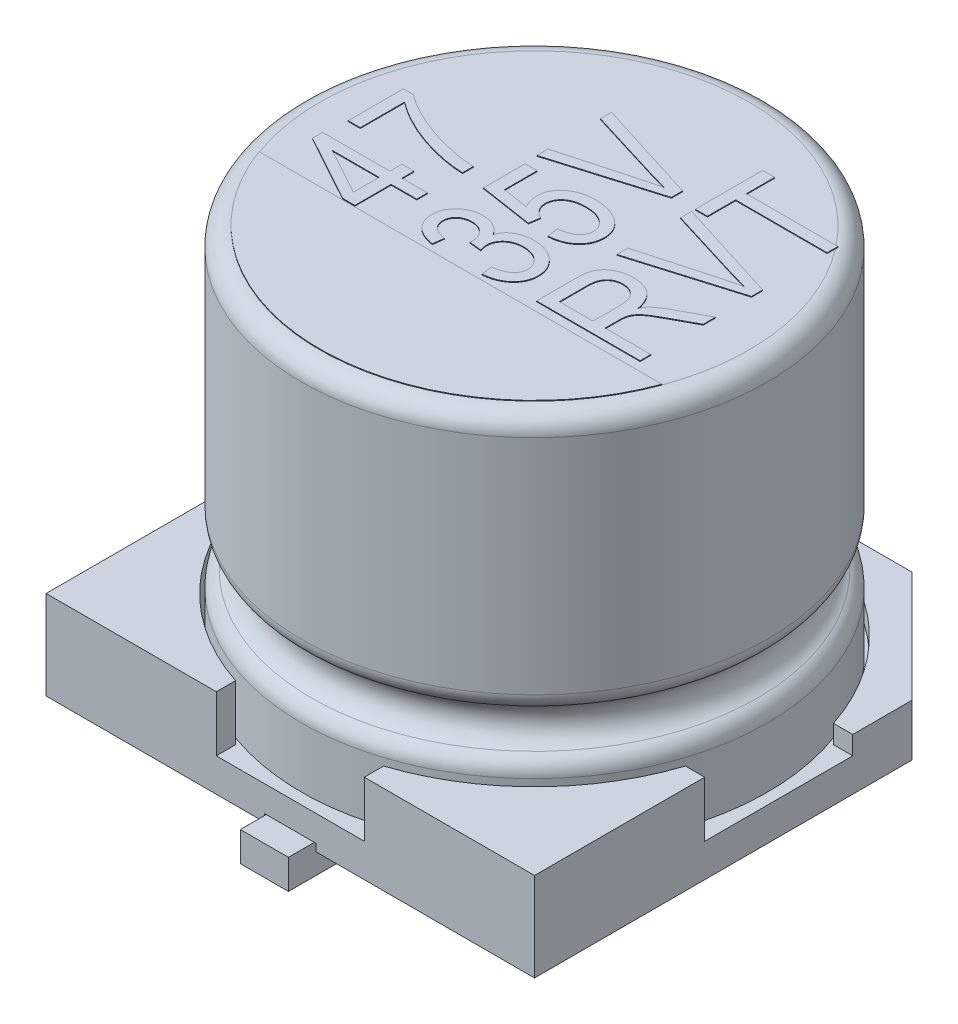
SolidWorks part; units mm, degrees
material "PA Type 6"
ref_plane "Front Plane" through (0, 0, 0) normal (0, 0, 1) x (1, 0, 0)
ref_plane "Top Plane" through (0, 0, 0) normal (0, 1, 0) x (1, 0, 0)
ref_plane "Right Plane" through (0, 0, 0) normal (1, 0, 0) x (0, 0, -1)
ref_plane "Plane1" through (0, 0.3, 0) normal (0, 1, 0) x (1, 0, 0)
sketch "Sketch1" plane through (0, 0.3, 0) normal (0, 1, 0) x (1, 0, 0)
  line L0 (-55, 0) -> (55, 0) construction
  line L1 (-3.3, -3.3) -> (3.3, -3.3)
  line L2 (-3.3, -3.3) -> (-3.3, 3.3)
  line L3 (-3.3, 3.3) -> (3.3, 3.3)
  line L4 (3.3, -3.3) -> (3.3, 3.3)
  line L5 (0, -55) -> (0, 55) construction
  dimension "D1" = 6.6
  dimension "D2" = 6.6
  dimension "D3" = 3.3
  dimension "D4" = 3.3
extrude "Boss-Extrude1" add sketch "Sketch1" along normal blind 1.2
sketch "Sketch2" plane through (0, 1.5, 0) normal (0, 1, 0) x (1, 0, 0)
  line L0 (-3.3, 1) -> (-3.0397, 1)
  line L1 (-3.3, 3.3) -> (-3.3, -3.3) construction
  line L2 (3.3, -3.3) -> (3.3, 3.3) construction
  line L3 (3.3, 1) -> (3.3, -1)
  line L4 (3.3, -1) -> (3.0397, -1)
  line L5 (-3.3, -1) -> (-3.3, 1)
  line L6 (3.3, 3.3) -> (-3.3, 3.3) construction
  line L7 (-1, 3.3) -> (1, 3.3)
  line L8 (-1, 3.3) -> (-1, 3.0397)
  line L9 (-1, -3.3) -> (1, -3.3)
  line L10 (1, 3.3) -> (1, 3.0397)
  line L11 (-3.3, -3.3) -> (3.3, -3.3) construction
  line L15 (-3.0397, -1) -> (-3.3, -1)
  line L16 (-1, -3.0397) -> (-1, -3.3)
  line L17 (1, -3.0397) -> (1, -3.3)
  line L19 (3.0397, 1) -> (3.3, 1)
  line L20 (-55, 0) -> (55, 0) construction
  line L22 (0, -55) -> (0, 55) construction
  arc A0 (3.0397, 1) -> (1, 3.0397) centre (0, 0) ccw
  arc A1 (-1, 3.0397) -> (-3.0397, 1) centre (0, 0) ccw
  arc A2 (-3.0397, -1) -> (-1, -3.0397) centre (0, 0) ccw
  arc A3 (1, -3.0397) -> (3.0397, -1) centre (0, 0) ccw
  dimension "D1" = 6.4
  dimension "D2" = 1
  dimension "D3" = 1
  dimension "D4" = 1
extrude "Cut-Extrude1" cut sketch "Sketch2" against normal blind 0.75
sketch "Sketch3" plane through (0, 0, 0) normal (1, 0, 0) x (0, 0, -1)
  line L0 (0, 55) -> (0, -55) construction
  line L1 (3.3, 1.5) -> (0, 1.5)
  line L2 (3.3, 1.5) -> (3.3, 1)
  line L3 (3.3, 1) -> (0, 1)
  line L4 (0, 1.5) -> (0, 1)
  dimension "D1" = 0.5
extrude "Cut-Extrude2" cut sketch "Sketch3" against normal through all and the other way through all
chamfer "Chamfer1" distance 1.5 angle 45 2 edges at (-3.3, 0.65, -3.3) (3.3, 0.65, -3.3)
sketch "Sketch4" plane through (0, 0, 0) normal (1, 0, 0) x (0, 0, -1)
  line L0 (0, 0) -> (0, 7.4696) construction
  line L1 (0, 55) -> (0, -55) construction
  line L2 (0, 0.75) -> (0, 5.8)
  line L3 (-1, 0.75) -> (1, 0.75) construction
  line L4 (0, 5.8) -> (-2.9, 5.8)
  line L5 (-3.15, 5.55) -> (-3.15, 2.5399)
  line L6 (-3.15, 1.5601) -> (-3.15, 0.75)
  line L7 (-3.15, 0.75) -> (0, 0.75)
  line L9 (55, 0) -> (-55, 0) construction
  arc A0 (-2.9, 5.8) -> (-3.15, 5.55) centre (-2.9, 5.55) ccw
  arc A1 (-3.0136, 2.3172) -> (-3.0136, 1.7828) centre (-3.15, 2.05) cw
  arc A2 (-3.0136, 1.7828) -> (-3.15, 1.5601) centre (-2.9, 1.5601) ccw
  arc A3 (-3.15, 2.5399) -> (-3.0136, 2.3172) centre (-2.9, 2.5399) ccw
  point P20 (-3.15, 1.75)
  dimension "D2" = 0.3
  dimension "D5" = 0.25
  dimension "D6" = 0.25
  dimension "D1" = 6.3
  dimension "D3" = 1
  dimension "D4" = 5.8
revolve "Revolve1" add sketch "Sketch4" angle 360 about L0
sketch "Sketch6" plane through (0, 0.3, 0) normal (0, -1, 0) x (1, 0, 0)
  line L0 (0, -55) -> (0, 55) construction
  line L1 (-0.325, -1.225) -> (-0.325, -3.65)
  line L2 (-0.325, -3.65) -> (0.325, -3.65)
  line L3 (0.325, -3.65) -> (0.325, -1.225)
  line L4 (-0.325, 1.225) -> (-0.325, 3.65)
  line L5 (-0.325, 3.65) -> (0.325, 3.65)
  line L6 (0.325, 3.65) -> (0.325, 1.225)
  line L7 (55, 0) -> (-55, 0) construction
  line L8 (-3.3, 3.3) -> (3.3, 3.3) construction
  line L9 (1.8, -3.3) -> (-1.8, -3.3) construction
  arc A0 (-0.325, 1.225) -> (0.325, 1.225) centre (0, 1.225) ccw
  arc A1 (0.325, -1.225) -> (-0.325, -1.225) centre (0, -1.225) ccw
  dimension "D1" = 0.65
  dimension "D2" = 2.45
  dimension "D3" = 1.225
  dimension "D4" = 0.35
  dimension "D5" = 0.35
sketch "Sketch7" plane through (0, 0.3, 0) normal (0, -1, 0) x (1, 0, 0)
  line L0 (-0.35, 3.3) -> (0.35, 3.3)
  line L1 (-3.3, 3.3) -> (3.3, 3.3) construction
  line L2 (0.35, 3.3) -> (0.4987, 1.2614)
  line L3 (-0.4987, 1.2614) -> (-0.35, 3.3)
  line L4 (-0.35, -3.3) -> (0.35, -3.3)
  line L5 (1.8, -3.3) -> (-1.8, -3.3) construction
  line L6 (-0.4987, -1.2614) -> (-0.35, -3.3)
  line L7 (0.4987, -1.2614) -> (0.35, -3.3)
  line L8 (0, -55) -> (0, 55) construction
  arc A0 (-0.4987, 1.2614) -> (0.4987, 1.2614) centre (0, 1.225) ccw
  arc A1 (0.4987, -1.2614) -> (-0.4987, -1.2614) centre (0, -1.225) ccw
  dimension "D3" = 1
  dimension "D1" = 0.7
  dimension "D2" = 0.35
extrude "Cut-Extrude3" cut sketch "Sketch7" against normal blind 0.1
extrude "Boss-Extrude4" add sketch "Sketch6" against normal blind 0.1 and the other way blind 0.3
sketch "Sketch8" plane through (0, 0.3, 0) normal (0, -1, 0) x (1, 0, 0)
  line L0 (0, -55) -> (0, 55) construction
  line L1 (-2, 2) -> (2, 2) construction
  line L2 (-2, 2) -> (-2, -2) construction
  line L3 (-2, -2) -> (2, -2) construction
  line L4 (2, 2) -> (2, -2) construction
  line L5 (55, 0) -> (-55, 0) construction
  circle A0 centre (-2, 2) radius 0.5
  circle A1 centre (2, 2) radius 0.5
  circle A2 centre (2, -2) radius 0.5
  circle A3 centre (-2, -2) radius 0.5
  dimension "D1" = 1
  dimension "D2" = 2
  dimension "D3" = 2
  dimension "D4" = 2
  dimension "D5" = 2
extrude "Boss-Extrude5" add sketch "Sketch8" along normal blind 0.3
sketch "Sketch10" plane through (0, 5.8, 0) normal (0, 1, 0) x (1, 0, 0)
  line L0 (-2.7221, -1) -> (2.7221, -1)
  line L1 (-3.19, 0) -> (3.19, 0) construction
  line L2 (-1.1, -1) -> (-1.1, 2) construction
  line L3 (0, -3.19) -> (0, 3.19) construction
  line L4 (0.6, -1) -> (0.6, 2) construction
  line L6 (2.3, -1) -> (2.3, 2) construction
  circle A0 centre (0, 0) radius 2.9 construction
  arc A1 (-2.7221, -1) -> (2.7221, -1) centre (0, 0) ccw
  text T0 "47" font "Arial Narrow" height 1.4
  text T1 "35V" font "Arial Narrow" height 1.4
  text T2 "RVT\r\n" font "Arial Narrow" height 1.4
  dimension "D1" = 1
  dimension "D2" = 1.1
  dimension "D3" = 1.7
  dimension "D4" = 1.7
  dimension "D5" = 3
extrude "Boss-Extrude7" add sketch "Sketch10" along normal blind 0.01
